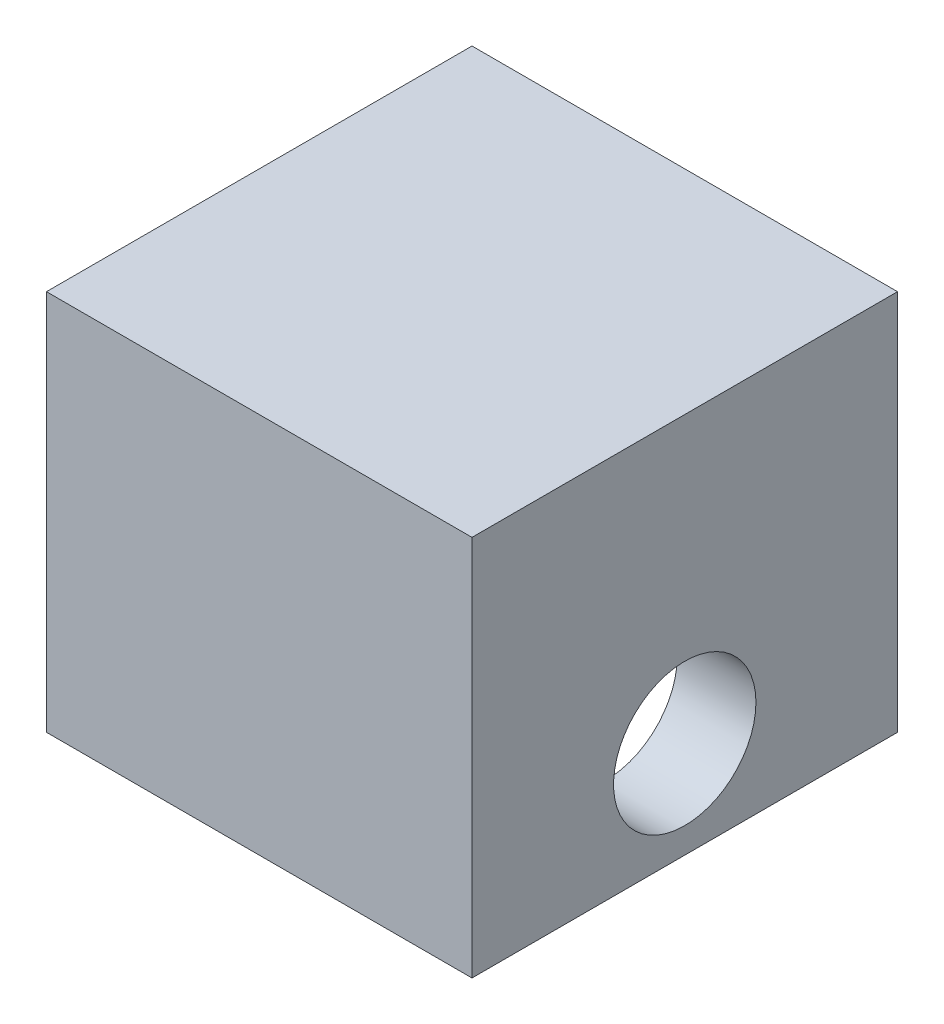
SolidWorks part; units mm, degrees
ref_plane "Front Plane" through (0, 0, 0) normal (0, 0, 1) x (1, 0, 0)
ref_plane "Top Plane" through (0, 0, 0) normal (0, 1, 0) x (1, 0, 0)
ref_plane "Right Plane" through (0, 0, 0) normal (1, 0, 0) x (0, 0, -1)
sketch "Sketch1" plane through (0, 0, 0) normal (0, 0, 1) x (1, 0, 0)
  line L0 (0, 0) -> (0, 10.0889)
  line L1 (0, 10.0889) -> (8.001, 10.0889)
  line L2 (8.001, 10.0889) -> (8.001, 0)
  line L3 (8.001, 0) -> (10.3505, 0)
  line L6 (10.3505, 0) -> (10.3505, 12.0879)
  line L7 (10.3505, 12.0879) -> (-2.3495, 12.0879)
  line L8 (-2.3495, 12.0879) -> (-2.3495, 0)
  line L9 (-2.3495, 0) -> (0, 0)
  dimension "D1" = 10.0889
  dimension "D2" = 8.001
  dimension "D3" = 2.3495
  dimension "D4" = 12.7
extrude "Boss-Extrude1" add sketch "Sketch1" along normal blind 10.795
sketch "Sketch2" plane through (10.3505, 0, 0) normal (1, 0, 0) x (0, 0, -1)
  line L0 (0, 0) -> (0, 12.0879) construction
  circle A0 centre (-5.3975, 3.5865) radius 2.1247
  dimension "D2" = 4.2494
  dimension "D1" = 5.3975
extrude "Cut-Extrude1" cut sketch "Sketch2" against normal through all
sketch "Sketch3" plane through (10.3505, 0, 0) normal (1, 0, 0) x (0, 0, -1)
  line L0 (-10.795, 0) -> (-10.795, 0.6985)
  line L1 (-10.795, 0) -> (-10.795, 12.0879) construction
  line L2 (-10.795, 0.6985) -> (0, 0.6985)
  line L3 (0, 0) -> (0, 12.0879) construction
  line L4 (0, 0.6985) -> (0, 0)
  line L5 (0, 0) -> (-10.795, 0)
  dimension "D1" = 0.6985
extrude "Cut-Extrude2" cut sketch "Sketch3" against normal through all
sketch "Sketch4" plane through (10.3505, 0, 0) normal (1, 0, 0) x (0, 0, -1)
  line L0 (-10.795, 12.0879) -> (-11.7475, 12.0879)
  line L1 (-11.7475, 12.0879) -> (-11.7475, 0.6985)
  line L2 (-11.7475, 0.6985) -> (-10.795, 0.6985)
  line L3 (-10.795, 0.6985) -> (-10.795, 12.0879)
  line L4 (0, 12.0879) -> (0.9525, 12.0879)
  line L5 (0.9525, 12.0879) -> (0.9525, 0.6985)
  line L6 (0.9525, 0.6985) -> (0, 0.6985)
  line L7 (0, 12.0879) -> (0, 0.6985)
  dimension "D1" = 0.9525
  dimension "D2" = 0.9525
extrude "Boss-Extrude2" add sketch "Sketch4" against normal blind 12.7
